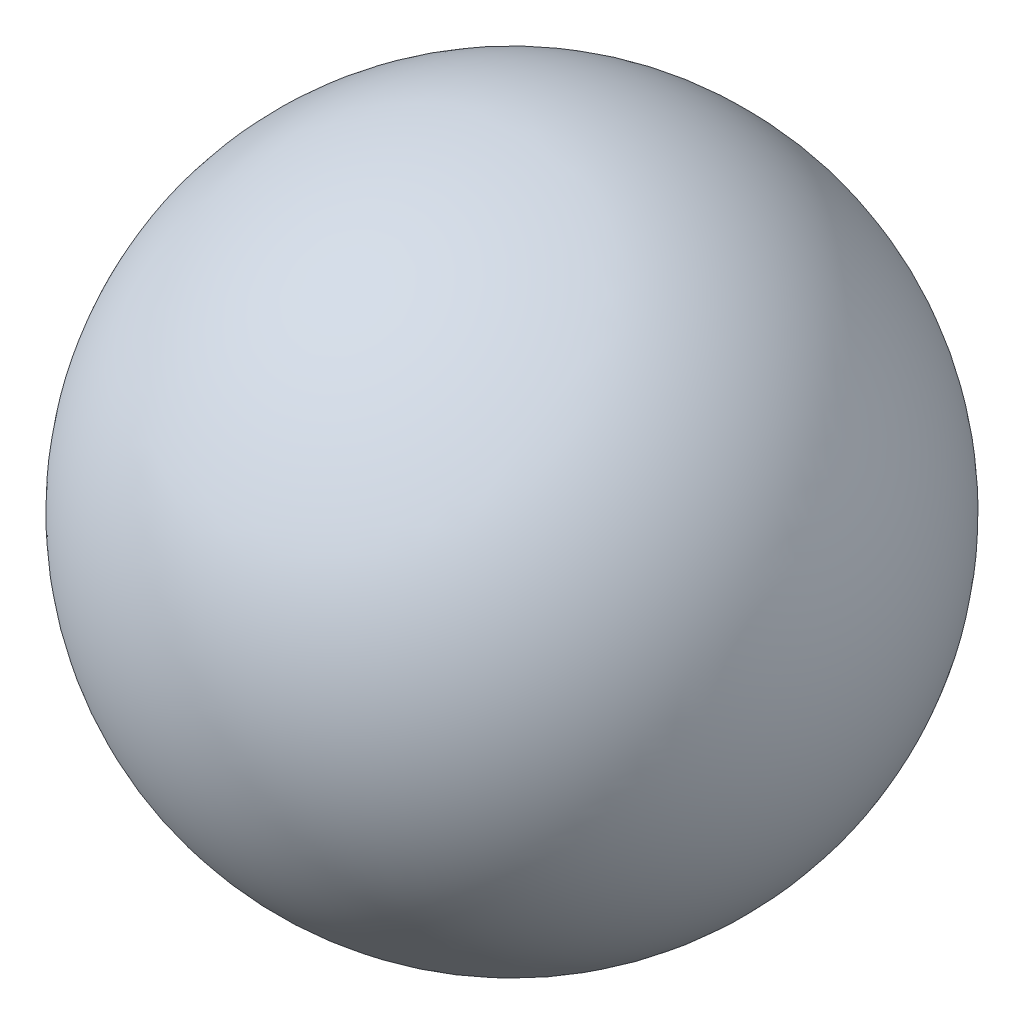
SolidWorks part; units mm, degrees
material "Chrome Stainless Steel"
ref_plane "Front Plane" through (0, 0, 0) normal (0, 0, 1) x (1, 0, 0)
ref_plane "Top Plane" through (0, 0, 0) normal (0, 1, 0) x (1, 0, 0)
ref_plane "Right Plane" through (0, 0, 0) normal (1, 0, 0) x (0, 0, -1)
sketch "Sketch1" plane through (0, 0, 0) normal (0, 0, 1) x (1, 0, 0)
  line L0 (-2.25, 0) -> (2.25, 0)
  arc A0 (2.25, 0) -> (-2.25, 0) centre (0, 0) cw
  point P4 (0, 0)
  dimension "D1" = 4.5
revolve "Revolve1" add sketch "Sketch1" angle 360 about L0
